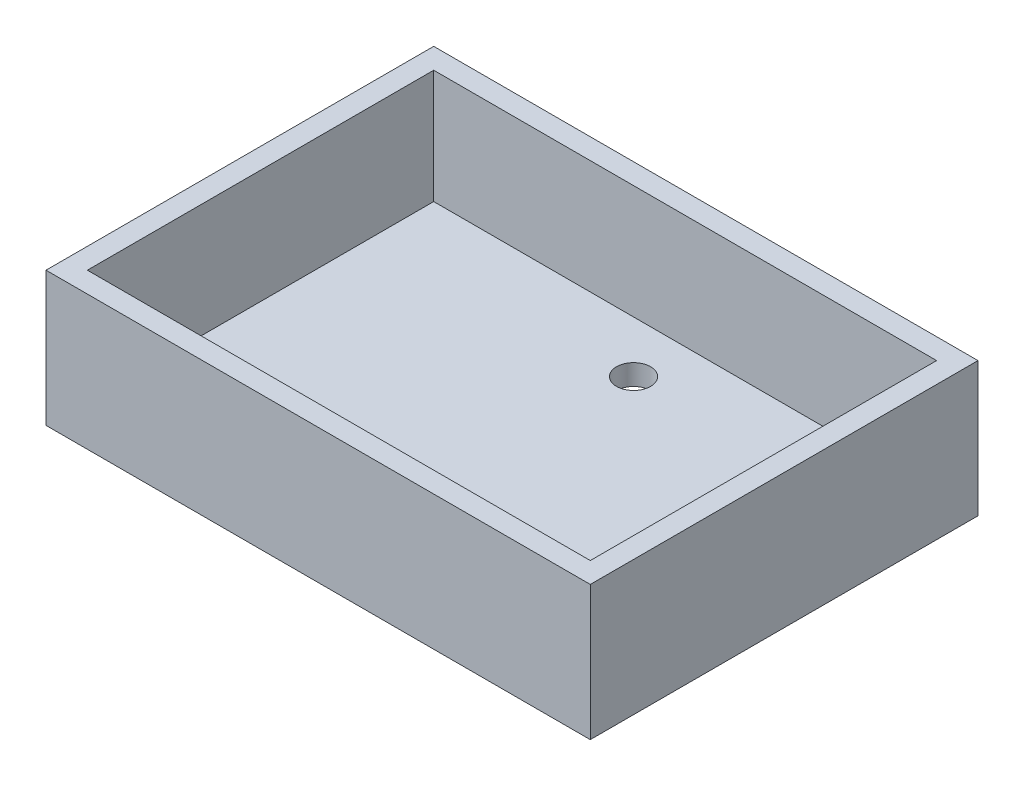
SolidWorks part; units mm, degrees
ref_plane "Front Plane" through (0, 0, 0) normal (0, 0, 1) x (1, 0, 0)
ref_plane "Top Plane" through (0, 0, 0) normal (0, 1, 0) x (1, 0, 0)
ref_plane "Right Plane" through (0, 0, 0) normal (1, 0, 0) x (0, 0, -1)
sketch "Sketch1" plane through (0, 0, 0) normal (0, 1, 0) x (1, 0, 0)
  line L1 (26.315, -18.745) -> (-26.315, -18.745)
  line L2 (26.315, -18.745) -> (26.315, 18.745)
  line L3 (26.315, 18.745) -> (-26.315, 18.745)
  line L4 (-26.315, -18.745) -> (-26.315, 18.745)
  line L5 (26.315, -18.745) -> (-26.315, 18.745) construction
  line L6 (26.315, 18.745) -> (-26.315, -18.745) construction
  circle A0 centre (0, 11.755) radius 1.65
  circle A1 centre (0, -11.745) radius 1.7077
  point P0 (0, 0)
  dimension "D3" = 23.5
  dimension "D1" = 52.63
  dimension "D2" = 37.49
  dimension "D4" = 7
extrude "Boss-Extrude1" add sketch "Sketch1" along normal blind 13
sketch "Sketch3" plane through (0, 13, 0) normal (0, 1, 0) x (1, 0, 0)
  line L0 (-26.315, 18.745) -> (-26.315, -18.745) construction
  line L1 (24.315, -16.745) -> (-24.315, -16.745)
  line L2 (24.315, -16.745) -> (24.315, 16.745)
  line L3 (24.315, 16.745) -> (-24.315, 16.745)
  line L4 (-24.315, -16.745) -> (-24.315, 16.745)
  line L5 (24.315, -16.745) -> (-24.315, 16.745) construction
  line L6 (24.315, 16.745) -> (-24.315, -16.745) construction
  line L7 (26.315, 18.745) -> (-26.315, 18.745) construction
  point P0 (0, 0)
  dimension "D1" = 2
  dimension "D2" = 2
extrude "Cut-Extrude2" cut sketch "Sketch3" against normal blind 11
